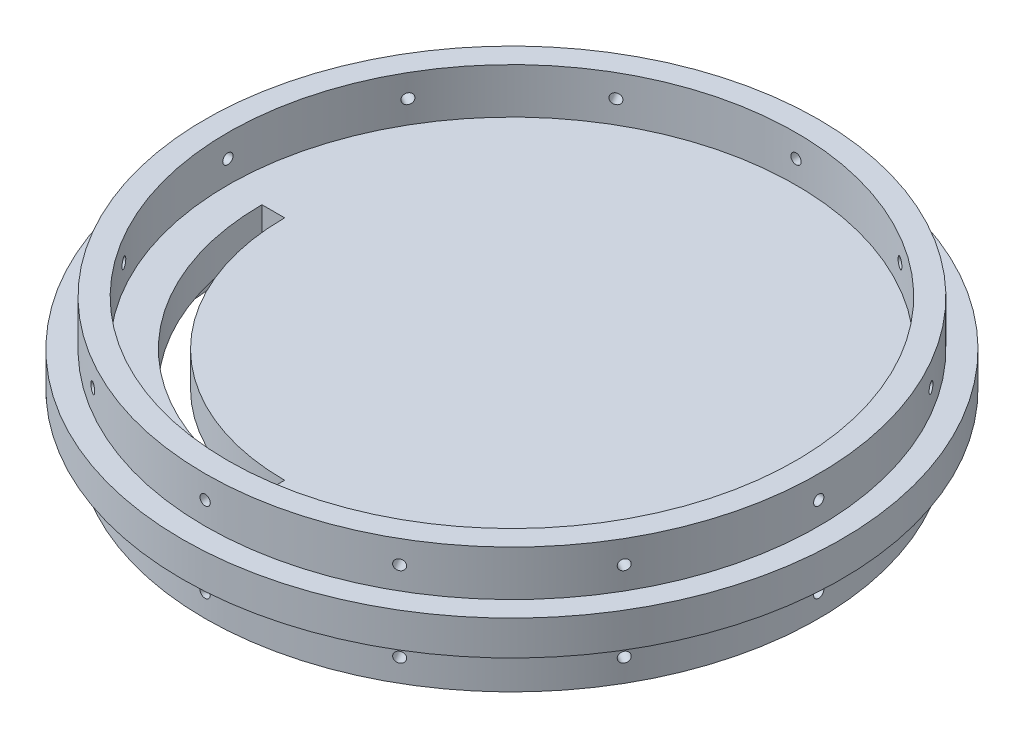
SolidWorks part; units mm, degrees
material "6061-T6 (SS)"
ref_plane "Front Plane" through (0, 0, 0) normal (0, 0, 1) x (1, 0, 0)
ref_plane "Top Plane" through (0, 0, 0) normal (0, 1, 0) x (1, 0, 0)
ref_plane "Right Plane" through (0, 0, 0) normal (1, 0, 0) x (0, 0, -1)
sketch "Sketch1" plane through (0, 0, 0) normal (0, 1, 0) x (1, 0, 0)
  circle A0 centre (0, 0) radius 92.075
  dimension "D1" = 184.15
extrude "Boss-Extrude1" add sketch "Sketch1" along normal mid plane 9.652
sketch "Sketch2" plane through (0, 0, 0) normal (0, 0, 1) x (1, 0, 0)
  line L0 (0, -18.3275) -> (0, 20.8308) construction
  line L1 (0, -4.826) -> (-19.297, -4.826)
  line L2 (-92.075, -4.826) -> (92.075, -4.826) construction
  line L3 (0, -4.826) -> (0, -1.4952)
  line L4 (-0.3818, -1.4952) -> (0, -1.4952)
  arc A0 (-19.297, -4.826) -> (-0.3818, -1.4952) centre (-0.4072, -56.7254) cw
  dimension "D6" = 55.2302
  dimension "D1" = 19.297
  dimension "D2" = 3.3308
  dimension "D3" = 0.3818
revolve "Cut-Revolve1" cut sketch "Sketch2" angle 360 about L0
sketch "Sketch4" plane through (0, 4.826, 0) normal (0, 1, 0) x (1, 0, 0)
  circle A0 centre (0, 0) radius 85.725
  circle A1 centre (0, 0) radius 79.375
  dimension "D1" = 171.45
  dimension "D2" = 158.75
extrude "Boss-Extrude2" add sketch "Sketch4" along normal blind 12.7
ref_plane "Plane1" through (0, 0, -85.725) normal (0, 0, -1) x (-1, 0, 0)
sketch "Sketch5" plane through (0, 0, -85.725) normal (0, 0, -1) x (-1, 0, 0)
  line L0 (0, 55) -> (0, -55) construction
  line L1 (79.375, 17.526) -> (-79.375, 17.526) construction
  circle A0 centre (0, 11.176) radius 1.4351
  dimension "D1" = 2.8702
  dimension "D2" = 6.35
extrude "Cut-Extrude2" cut sketch "Sketch5" against normal blind 12.7
pattern_circular "CirPattern1" count 12 over 360 about axis through (0, 17.526, 0) along (0, -1, 0) of "Cut-Extrude2"
mirror "Mirror2" about plane through (0, 0, 0) normal (0, 1, 0) of "CirPattern1", "Cut-Extrude2", "Boss-Extrude2"
sketch "Sketch6" plane through (0, 4.826, 0) normal (0, 1, 0) x (1, 0, 0)
  line L0 (-63.5, 0) -> (-69.85, 0)
  line L1 (0, -69.85) -> (0, -63.5)
  line L2 (0, -55) -> (0, 55) construction
  arc A0 (-69.85, 0) -> (0, -69.85) centre (0, 0) ccw
  arc A1 (-63.5, 0) -> (0, -63.5) centre (0, 0) ccw
  dimension "D1" = 69.85
  dimension "D2" = 63.5
  dimension "D3" = 90
extrude "Cut-Extrude3" cut sketch "Sketch6" against normal up to surface (9.652 mm away) up to face at (0, -4.826, -19.297)
